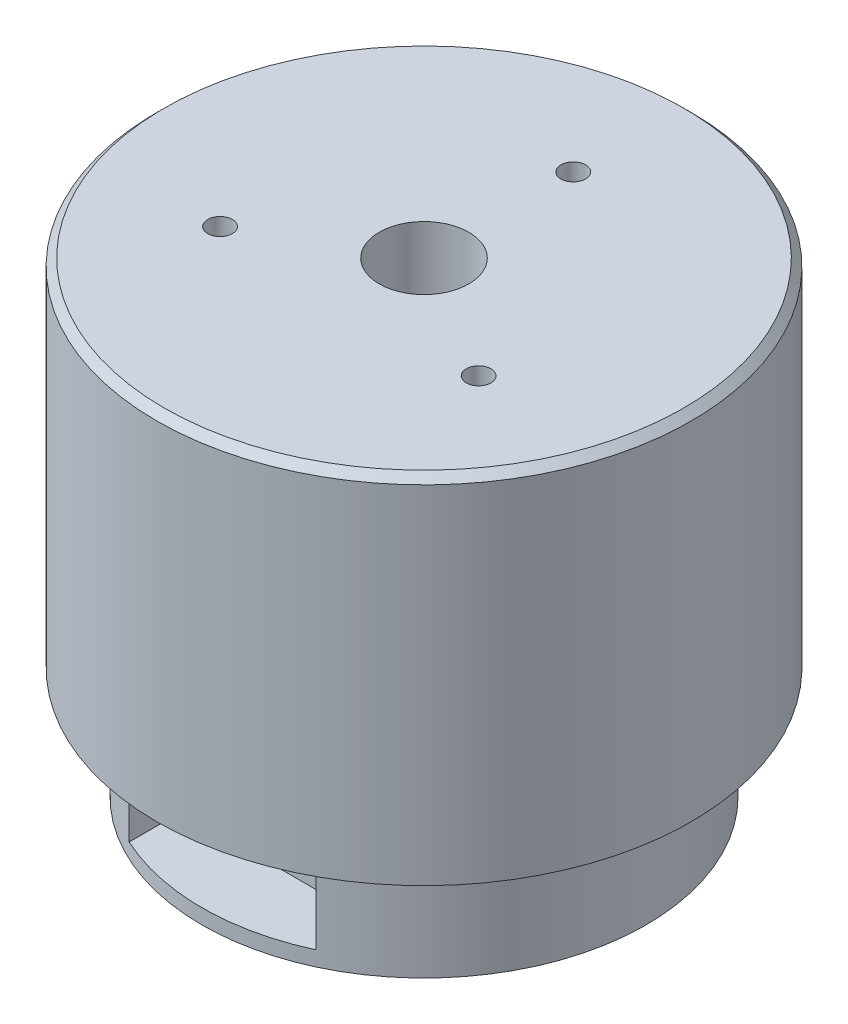
SolidWorks part; units mm, degrees
ref_plane "Front Plane" through (0, 0, 0) normal (0, 0, 1) x (1, 0, 0)
ref_plane "Top Plane" through (0, 0, 0) normal (0, 1, 0) x (1, 0, 0)
ref_plane "Right Plane" through (0, 0, 0) normal (1, 0, 0) x (0, 0, -1)
sketch "Sketch1" plane through (0, 0, 0) normal (0, 1, 0) x (1, 0, 0)
  circle A0 centre (0, 0) radius 29.75
  dimension "D1" = 59.5
extrude "Boss-Extrude1" add sketch "Sketch1" along normal blind 16
sketch "Sketch2" plane through (0, 16, 0) normal (0, 1, 0) x (1, 0, 0)
  circle A0 centre (0, 0) radius 35.8
  dimension "D1" = 71.6
extrude "Boss-Extrude2" add sketch "Sketch2" along normal blind 47.5
hole_wizard "M4 Tapped Hole1" positions "Sketch3" profile "Sketch4" tap size "M4" standard "ISO"
sketch "Sketch3" plane through (0, 63.5, 0) normal (0, 1, 0) x (1, 0, 0)
  line L1 (17.3205, -10) -> (0, 0) construction
  line L2 (0, 0) -> (0, 20) construction
  line L3 (0, 0) -> (-17.3205, -10) construction
  circle A0 centre (0, 0) radius 20 construction
  point P5 (0, 20)
  point P7 (17.3205, -10)
  point P9 (-17.3205, -10)
  dimension "D1" = 40
  dimension "D2" = 120
sketch "Sketch4" plane through (0, 63.5, -20) normal (1, 0, 0) x (0, 0, 1)
  line L0 (0, 0) -> (0, 6.9914)
  line L1 (0, 6.9914) -> (1.65, 6)
  line L2 (1.65, 6) -> (1.65, 0)
  line L5 (1.65, 0) -> (0, 0)
  line L10 (0, 6.9914) -> (-1.65, 6) construction
  line L11 (0, -6.35) -> (0, 107.95) construction
  dimension "Tap Drill Dia." = 3.3
  dimension "Tap Drill Depth" = 6
  dimension "Drill Angle" = 118
cosmetic thread "Hole Thread1" parameters "D1"=4, "D2"=4
cosmetic thread "Hole Thread2" parameters "D1"=4, "D2"=4
cosmetic thread "Hole Thread3" parameters "D1"=4, "D2"=4
sketch "Sketch6" plane through (0, 63.5, 0) normal (0, 1, 0) x (1, 0, 0)
  circle A0 centre (0, 0) radius 6
  dimension "D1" = 12
extrude "Cut-Extrude1" cut sketch "Sketch6" against normal blind 20
chamfer "Chamfer1" distance 1 angle 45 1 edges at (0, 63.5, 35.8)
chamfer "Chamfer2" distance 1 angle 75 1 edges at (0, 0, 29.75)
sketch "Sketch7" plane through (0, 0, 0) normal (0, 0, 1) x (1, 0, 0)
  line L0 (-29.75, 16) -> (29.75, 16) construction
  line L1 (-12.5, 16) -> (12.5, 16)
  line L2 (-12.5, 16) -> (-12.5, 3)
  line L3 (-12.5, 3) -> (12.5, 3)
  line L4 (12.5, 16) -> (12.5, 3)
  line L5 (-26.0179, 0) -> (26.0179, 0) construction
  line L6 (0, 0) -> (0, 16) construction
  dimension "D1" = 25
  dimension "D2" = 3
extrude "Cut-Extrude2" cut sketch "Sketch7" along normal blind 20 from offset 20
